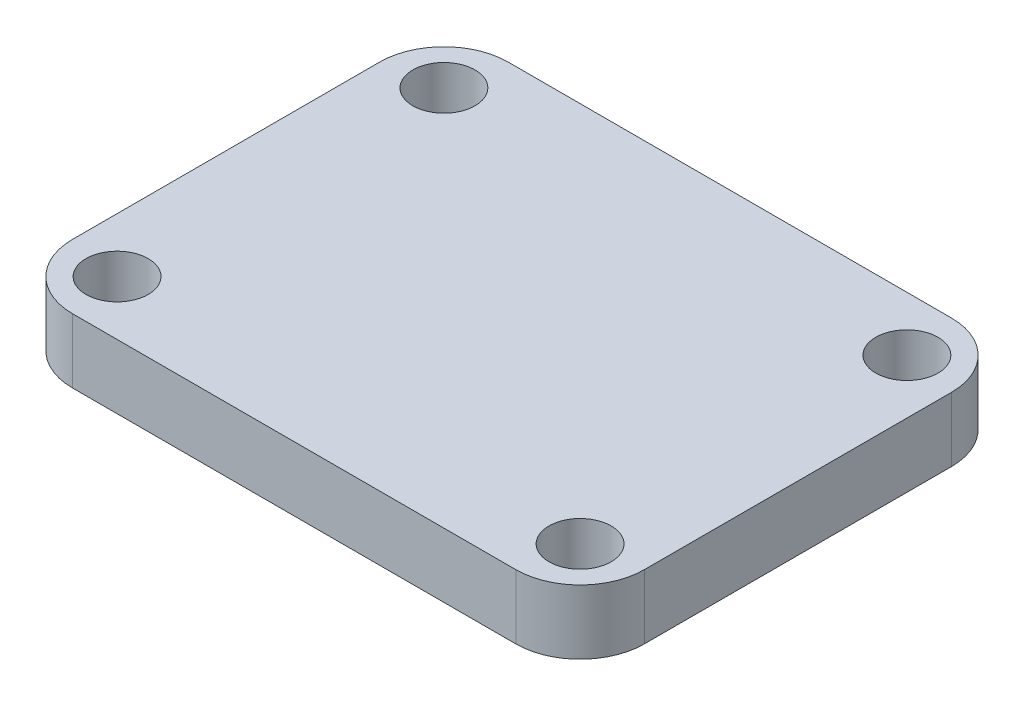
SolidWorks part; units mm, degrees
ref_plane "Front Plane" through (0, 0, 0) normal (0, 0, 1) x (1, 0, 0)
ref_plane "Top Plane" through (0, 0, 0) normal (0, 1, 0) x (1, 0, 0)
ref_plane "Right Plane" through (0, 0, 0) normal (1, 0, 0) x (0, 0, -1)
sketch "Sketch1" plane through (0, 0, 0) normal (0, 1, 0) x (1, 0, 0)
  line L1 (-13.335, -10.16) -> (13.335, -10.16)
  line L2 (-13.335, -10.16) -> (-13.335, 10.16)
  line L3 (-13.335, 10.16) -> (13.335, 10.16)
  line L4 (13.335, -10.16) -> (13.335, 10.16)
  line L5 (-13.335, -10.16) -> (13.335, 10.16) construction
  line L6 (-13.335, 10.16) -> (13.335, -10.16) construction
  line L7 (-10.795, -7.62) -> (10.795, -7.62) construction
  line L8 (-10.795, -7.62) -> (-10.795, 7.62) construction
  line L9 (-10.795, 7.62) -> (10.795, 7.62) construction
  line L10 (10.795, -7.62) -> (10.795, 7.62) construction
  line L11 (-10.795, -7.62) -> (10.795, 7.62) construction
  line L12 (-10.795, 7.62) -> (10.795, -7.62) construction
  circle A0 centre (-10.795, 7.62) radius 1.45
  circle A1 centre (-10.795, -7.62) radius 1.45
  circle A2 centre (10.795, -7.62) radius 1.45
  circle A3 centre (10.795, 7.62) radius 1.45
  point P0 (0, 0)
  point P6 (0, 0)
  dimension "D3" = 2.9
  dimension "D1" = 20.32
  dimension "D2" = 26.67
  dimension "D4" = 15.24
  dimension "D5" = 21.59
extrude "Boss-Extrude1" add sketch "Sketch1" along normal blind 3
fillet "Fillet1" radius 3 4 edges at (-13.335, 1.5, 10.16) (-13.335, 1.5, -10.16) (13.335, 1.5, -10.16) (13.335, 1.5, 10.16)
